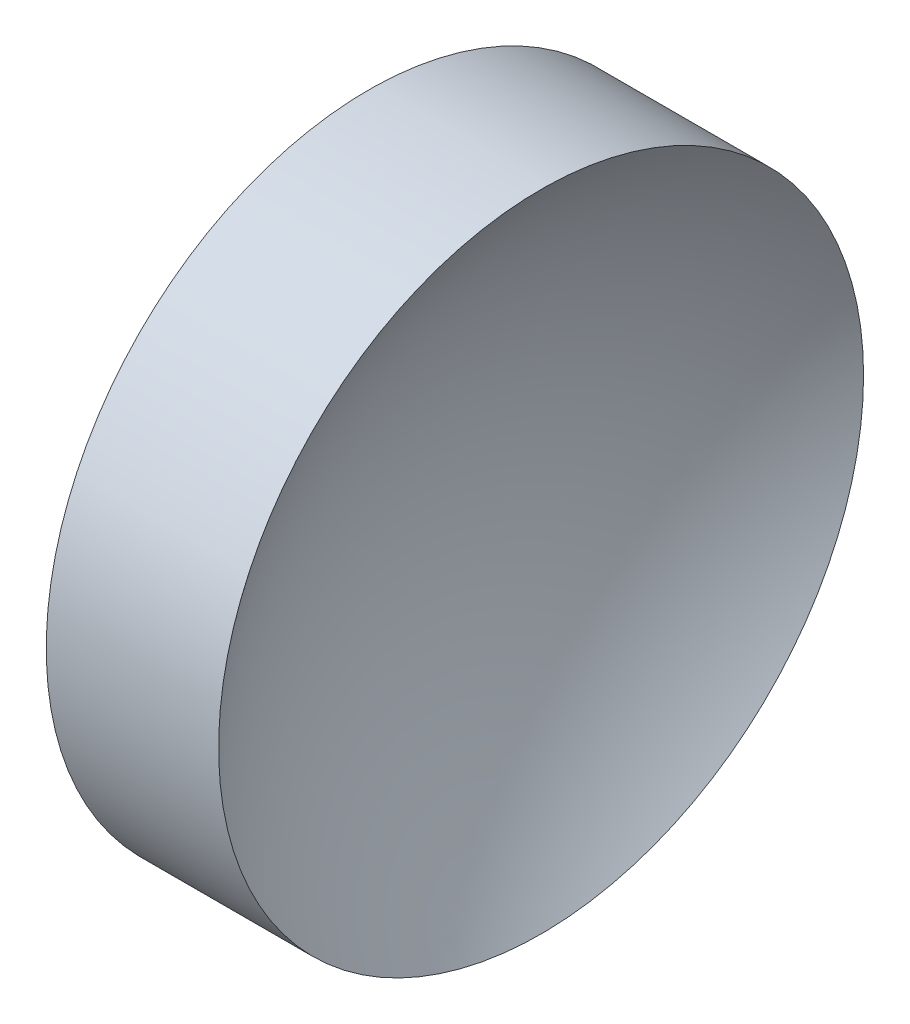
SolidWorks part; units mm, degrees
ref_plane "前视基准面" through (0, 0, 0) normal (0, 0, 1) x (1, 0, 0)
ref_plane "上视基准面" through (0, 0, 0) normal (0, 1, 0) x (1, 0, 0)
ref_plane "右视基准面" through (0, 0, 0) normal (1, 0, 0) x (0, 0, -1)
sketch "草图1" plane through (0, 0, 0) normal (0, 0, 1) x (1, 0, 0)
  line L0 (44.3192, 26.089) -> (44.3192, 34.089)
  line L1 (45.8192, 26.089) -> (44.3192, 26.089)
  line L3 (44.3192, 34.089) -> (48.5951, 34.089)
  line L4 (44.3192, 26.089) -> (38.5765, 26.089) construction
  line L5 (44.3192, 26.089) -> (47.8092, 26.089) construction
  arc A0 (48.5951, 34.089) -> (45.8192, 26.089) centre (58.7292, 26.091) ccw
revolve "旋转1" add sketch "草图1" angle 360 about L1
